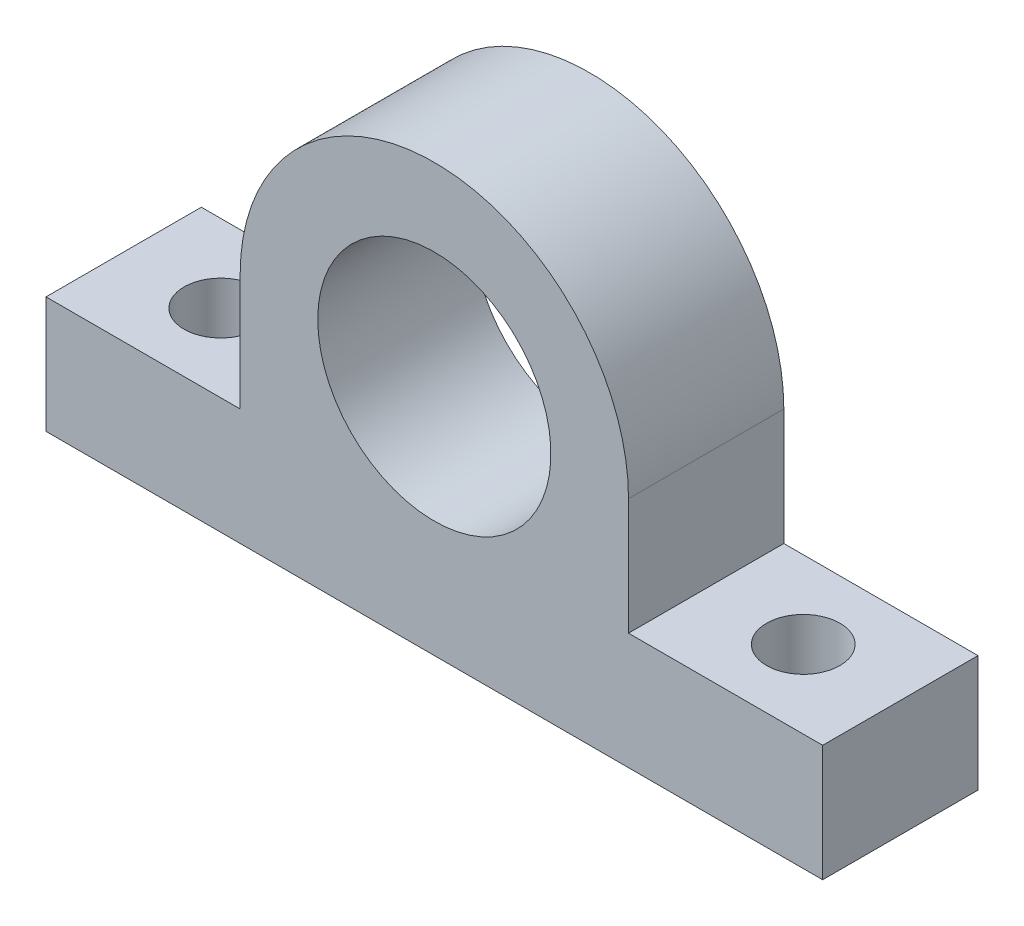
SolidWorks part; units mm, degrees
ref_plane "Front Plane" through (0, 0, 0) normal (0, 0, 1) x (1, 0, 0)
ref_plane "Top Plane" through (0, 0, 0) normal (0, 1, 0) x (1, 0, 0)
ref_plane "Right Plane" through (0, 0, 0) normal (1, 0, 0) x (0, 0, -1)
sketch "Sketch1" plane through (0, 0, 0) normal (0, 0, 1) x (1, 0, 0)
  line L0 (0, 28.575) -> (0, 9.525) construction
  line L1 (-63.5, -9.525) -> (63.5, -9.525)
  line L2 (-63.5, -9.525) -> (-63.5, 9.525)
  line L3 (-63.5, 9.525) -> (63.5, 9.525)
  line L4 (63.5, -9.525) -> (63.5, 9.525)
  line L5 (-63.5, -9.525) -> (63.5, 9.525) construction
  line L6 (-63.5, 9.525) -> (63.5, -9.525) construction
  line L7 (-31.75, 9.525) -> (31.75, 9.525)
  line L8 (-31.75, 9.525) -> (-31.75, 28.575)
  line L9 (-31.75, 28.575) -> (31.75, 28.575)
  line L10 (31.75, 9.525) -> (31.75, 28.575)
  arc A0 (-31.75, 28.575) -> (31.75, 28.575) centre (0, 28.575) cw
  point P0 (0, 0)
  dimension "D1" = 127
  dimension "D2" = 19.05
  dimension "D3" = 0
  dimension "D4" = 19.05
  dimension "D5" = 63.5
extrude "Boss-Extrude1" add sketch "Sketch1" along normal blind 25.4 contours A0 L9 | L3 L10 L9 L8 | L1 L4 L3 L2
sketch "Sketch5" plane through (0, 0, 0) normal (0, 0, -1) x (-1, 0, 0)
  line L0 (-31.75, 28.575) -> (31.75, 28.575) construction
  arc A0 (31.75, 28.575) -> (-31.75, 28.575) centre (0, 28.575) ccw construction
  circle A1 centre (0, 28.575) radius 19.0627
  dimension "D1" = 38.1254
extrude "Cut-Extrude1" cut sketch "Sketch5" against normal through all
sketch "Sketch6" plane through (0, 9.525, 0) normal (0, 1, 0) x (1, 0, 0)
  line L0 (-63.5, -12.7) -> (63.5, -12.7) construction
  line L1 (-63.5, -25.4) -> (-63.5, 0) construction
  line L2 (63.5, -25.4) -> (63.5, 0) construction
  line L3 (-47.625, -25.4) -> (-47.625, 0) construction
  line L4 (-63.5, -25.4) -> (-31.75, -25.4) construction
  line L5 (-63.5, 0) -> (-31.75, 0) construction
  line L6 (47.625, 0) -> (47.625, -25.4) construction
  line L7 (31.75, 0) -> (63.5, 0) construction
  line L8 (31.75, -25.4) -> (63.5, -25.4) construction
  point P18 (-47.625, -12.7)
  point P19 (47.625, -12.7)
hole_wizard "Ø12.0 (12) Diameter Hole1" positions "Sketch8" profile "Sketch7" hole size "Ø12.0" standard "ANSI Metric" end condition through all
sketch "Sketch8" plane through (0, 9.525, 0) normal (0, 1, 0) x (1, 0, 0)
  point P0 (-47.625, -12.7)
  point P3 (47.625, -12.7)
sketch "Sketch7" plane through (-47.625, 9.525, 12.7) normal (1, 0, 0) x (0, 0, 1)
  line L0 (0, 0) -> (0, 19.05)
  line L1 (0, 19.05) -> (6, 19.05)
  line L2 (6, 19.05) -> (6, 0)
  line L5 (6, 0) -> (0, 0)
  line L11 (0, -6.35) -> (0, 107.95) construction
  dimension "Thru Hole Dia." = 12
  dimension "Thru Hole Depth" = 19.05
